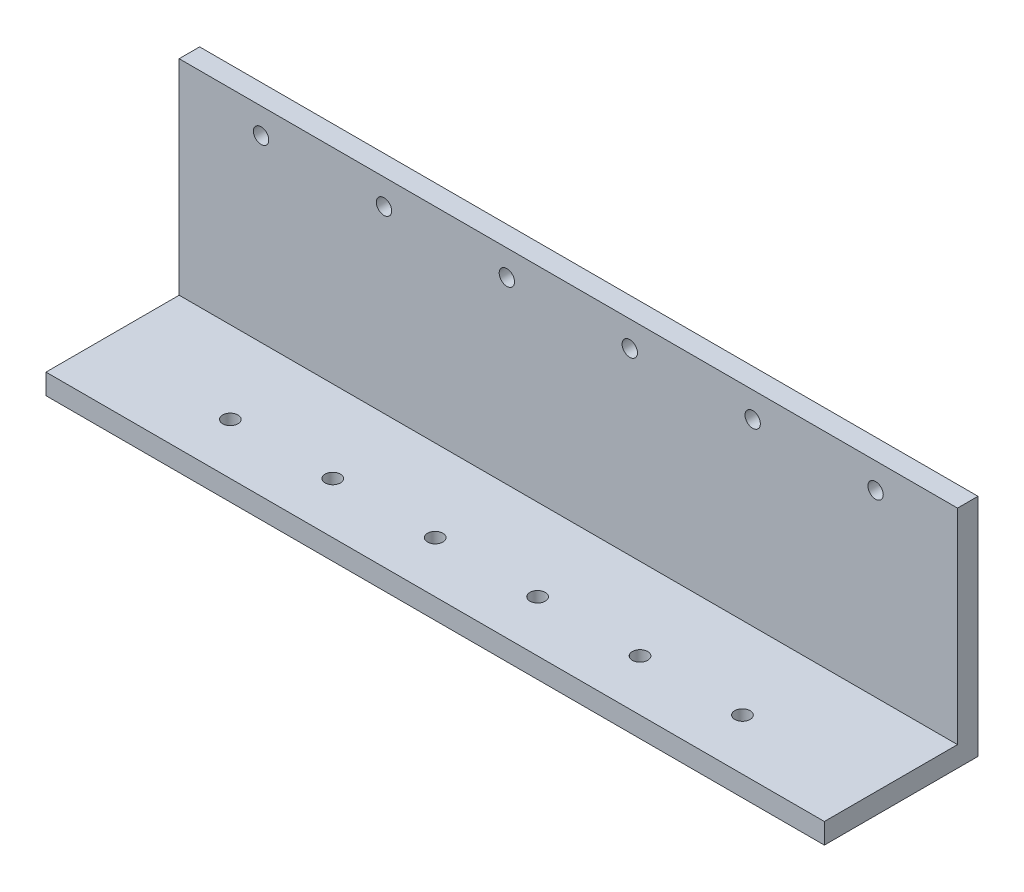
SolidWorks part; units mm, degrees
ref_plane "Front Plane" through (0, 0, 0) normal (0, 0, 1) x (1, 0, 0)
ref_plane "Top Plane" through (0, 0, 0) normal (0, 1, 0) x (1, 0, 0)
ref_plane "Right Plane" through (0, 0, 0) normal (1, 0, 0) x (0, 0, -1)
sketch "Sketch2" plane through (0, 0, 0) normal (0, 0, 1) x (1, 0, 0)
  line L0 (38, 20) -> (38, 17.5) construction
  line L1 (0, 0) -> (76, 0)
  line L2 (0, 0) -> (0, 20)
  line L3 (0, 20) -> (76, 20)
  line L4 (76, 0) -> (76, 20)
  line L5 (38, 17.5) -> (44, 17.5) construction
  line L6 (44, 17.5) -> (56, 17.5) construction
  line L7 (56, 17.5) -> (68, 17.5) construction
  line L8 (38, 17.5) -> (32, 17.5) construction
  line L9 (32, 17.5) -> (20, 17.5) construction
  line L10 (20, 17.5) -> (8, 17.5) construction
  circle A0 centre (44, 17.5) radius 0.75
  circle A1 centre (56, 17.5) radius 0.75
  circle A2 centre (68, 17.5) radius 0.75
  circle A3 centre (32, 17.5) radius 0.75
  circle A4 centre (20, 17.5) radius 0.75
  circle A5 centre (8, 17.5) radius 0.75
  point P16 (55.6962, 17.5)
  point P18 (67.6766, 17.5)
  point P20 (31.983, 17.5)
  point P22 (19.7551, 17.5)
  point P23 (0, 0)
  point P24 (7.7253, 17.5)
  point P25 (0, 0)
  point P26 (0, 0)
  point P27 (0, 0)
  point P28 (0, 0)
  point P29 (0, 0)
  point P30 (0, 0)
  point P31 (0, 0)
extrude "Boss-Extrude1" add sketch "Sketch2" along normal blind 2
ref_plane "Plane1" through (0, 0, 0) normal (0, -1, 0) x (-1, 0, 0)
sketch "Sketch3" plane through (0, 0, 0) normal (0, -1, 0) x (-1, 0, 0)
  line L0 (-38, 0) -> (-38, -10) construction
  line L1 (-76, 0) -> (0, 0)
  line L2 (-76, 0) -> (-76, -15)
  line L3 (-76, -15) -> (0, -15)
  line L4 (0, 0) -> (0, -15)
  line L5 (-38, -10) -> (-33, -10) construction
  line L6 (-33, -10) -> (-23, -10) construction
  line L7 (-23, -10) -> (-13, -10) construction
  line L8 (-38, -10) -> (-43, -10) construction
  line L9 (-43, -10) -> (-53, -10) construction
  line L10 (-53, -10) -> (-63, -10) construction
  circle A0 centre (-13, -10) radius 0.75
  circle A1 centre (-23, -10) radius 0.75
  circle A2 centre (-33, -10) radius 0.75
  circle A3 centre (-43, -10) radius 0.75
  circle A6 centre (-53, -10) radius 0.75
  circle A7 centre (-63, -10) radius 0.75
  point P12 (0, 0)
  point P13 (0, 0)
  point P16 (0, 0)
  point P20 (-53.4861, -10)
  point P22 (-63.5258, -10)
  point P23 (0, 0)
  point P24 (0, 0)
extrude "Boss-Extrude2" add sketch "Sketch3" along normal blind 2
